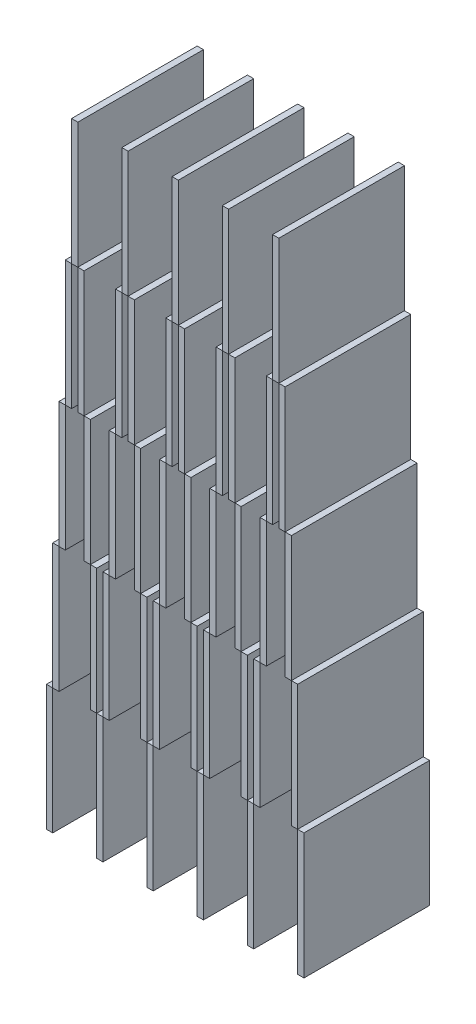
SolidWorks part; units mm, degrees
ref_plane "Front Plane" through (0, 0, 0) normal (0, 0, 1) x (1, 0, 0)
ref_plane "Top Plane" through (0, 0, 0) normal (0, 1, 0) x (1, 0, 0)
ref_plane "Right Plane" through (0, 0, 0) normal (1, 0, 0) x (0, 0, -1)
sketch "Sketch1" plane through (0, 0, 0) normal (0, 0, 1) x (1, 0, 0)
  line L361 (-45.534, 24.8846) -> (-44.534, 24.8846)
  line L362 (-46.534, 24.8846) -> (-45.534, 24.8846)
  line L363 (-46.534, 24.8846) -> (-46.534, 4.8846)
  line L364 (-46.534, 4.8846) -> (-45.534, 4.8846)
  line L365 (-45.534, 24.8846) -> (-45.534, 4.8846)
  line L366 (-45.534, 24.8846) -> (-44.534, 24.8846)
  line L367 (-45.534, 24.8846) -> (-45.534, 44.8846)
  line L368 (-45.534, 44.8846) -> (-44.534, 44.8846)
  line L369 (-44.534, 24.8846) -> (-44.534, 44.8846)
  line L371 (-44.534, 24.8846) -> (-44.534, 44.8846)
  line L372 (-44.534, 44.8846) -> (-43.534, 44.8846)
  line L374 (-38.534, 24.8846) -> (-37.534, 24.8846)
  line L379 (-38.534, 24.8846) -> (-38.534, 4.8846)
  line L384 (-38.534, 4.8846) -> (-37.534, 4.8846)
  line L389 (-37.534, 24.8846) -> (-37.534, 4.8846)
  line L392 (-40.534, 44.8846) -> (-39.534, 44.8846)
  line L393 (-39.534, 24.8846) -> (-39.534, 44.8846)
  line L394 (-37.534, 24.8846) -> (-36.534, 24.8846)
  line L395 (-39.534, 24.8846) -> (-38.534, 24.8846)
  line L396 (-39.534, 24.8846) -> (-39.534, 44.8846)
  line L397 (-39.534, 44.8846) -> (-38.534, 44.8846)
  line L398 (-38.534, 24.8846) -> (-38.534, 44.8846)
  line L399 (-45.534, 44.8846) -> (-44.534, 44.8846)
  line L400 (-45.534, 44.8846) -> (-44.534, 44.8846)
  line L403 (-44.534, 44.8846) -> (-44.534, 64.8846)
  line L404 (-44.534, 44.8846) -> (-43.534, 44.8846)
  line L405 (-44.534, 44.8846) -> (-44.534, 64.8846)
  line L406 (-44.534, 64.8846) -> (-43.534, 64.8846)
  line L407 (-43.534, 44.8846) -> (-43.534, 64.8846)
  line L408 (-44.534, 44.8846) -> (-43.534, 44.8846)
  line L410 (-43.534, 44.8846) -> (-43.534, 64.8846)
  line L411 (-43.534, 64.8846) -> (-42.534, 64.8846)
  line L413 (-37.534, 24.8846) -> (-36.534, 24.8846)
  line L418 (-37.534, 24.8846) -> (-37.534, 44.8846)
  line L421 (-41.534, 64.8846) -> (-40.534, 64.8846)
  line L422 (-40.534, 44.8846) -> (-40.534, 64.8846)
  line L423 (-37.534, 44.8846) -> (-36.534, 44.8846)
  line L424 (-40.534, 44.8846) -> (-39.534, 44.8846)
  line L425 (-40.534, 44.8846) -> (-40.534, 64.8846)
  line L426 (-40.534, 64.8846) -> (-39.534, 64.8846)
  line L427 (-39.534, 44.8846) -> (-39.534, 64.8846)
  line L428 (-40.534, 44.8846) -> (-39.534, 44.8846)
  line L429 (-39.534, 44.8846) -> (-38.534, 44.8846)
  line L430 (-39.534, 44.8846) -> (-39.534, 64.8846)
  line L433 (-36.534, 24.8846) -> (-36.534, 44.8846)
  line L438 (-44.534, 64.8846) -> (-43.534, 64.8846)
  line L441 (-43.534, 64.8846) -> (-43.534, 84.8846)
  line L442 (-44.534, 64.8846) -> (-43.534, 64.8846)
  line L443 (-43.534, 64.8846) -> (-42.534, 64.8846)
  line L444 (-43.534, 64.8846) -> (-43.534, 84.8846)
  line L445 (-43.534, 84.8846) -> (-42.534, 84.8846)
  line L446 (-42.534, 64.8846) -> (-42.534, 84.8846)
  line L447 (-43.534, 64.8846) -> (-42.534, 64.8846)
  line L449 (-42.534, 64.8846) -> (-42.534, 84.8846)
  line L450 (-42.534, 84.8846) -> (-41.534, 84.8846)
  line L451 (-41.534, 64.8846) -> (-41.534, 84.8846)
  line L452 (-36.534, 24.8846) -> (-36.534, 44.8846)
  line L453 (-41.534, 64.8846) -> (-40.534, 64.8846)
  line L454 (-41.534, 64.8846) -> (-41.534, 84.8846)
  line L455 (-41.534, 84.8846) -> (-40.534, 84.8846)
  line L456 (-40.534, 64.8846) -> (-40.534, 84.8846)
  line L457 (-41.534, 64.8846) -> (-40.534, 64.8846)
  line L458 (-40.534, 64.8846) -> (-39.534, 64.8846)
  line L459 (-40.534, 64.8846) -> (-40.534, 84.8846)
  line L462 (-40.534, 64.8846) -> (-39.534, 64.8846)
  line L467 (-36.534, 44.8846) -> (-35.534, 44.8846)
  line L476 (-32.534, 44.8846) -> (-31.534, 44.8846)
  line L477 (-43.534, 84.8846) -> (-42.534, 84.8846)
  line L480 (-42.534, 84.8846) -> (-42.534, 104.8846)
  line L481 (-43.534, 84.8846) -> (-42.534, 84.8846)
  line L482 (-42.534, 84.8846) -> (-41.534, 84.8846)
  line L483 (-42.534, 84.8846) -> (-42.534, 104.8846)
  line L484 (-42.534, 104.8846) -> (-41.534, 104.8846)
  line L485 (-41.534, 84.8846) -> (-41.534, 104.8846)
  line L486 (-42.534, 84.8846) -> (-41.534, 84.8846)
  line L487 (-41.534, 84.8846) -> (-40.534, 84.8846)
  line L488 (-41.534, 84.8846) -> (-41.534, 104.8846)
  line L491 (-41.534, 84.8846) -> (-40.534, 84.8846)
  line L496 (-31.534, 24.8846) -> (-31.534, 44.8846)
  line L501 (-44.534, 24.8846) -> (-43.534, 24.8846) [skipped]
  line L502 (-44.534, 24.8846) -> (-43.534, 24.8846) [skipped]
  line L503 (-43.534, 24.8846) -> (-43.534, 44.8846) [skipped]
  line L504 (-43.534, 24.8846) -> (-43.534, 44.8846) [skipped]
  line L505 (-42.534, 24.8846) -> (-42.534, 44.8846) [skipped]
  line L506 (-42.534, 24.8846) -> (-42.534, 44.8846) [skipped]
  line L507 (-41.534, 24.8846) -> (-41.534, 44.8846) [skipped]
  line L508 (-41.534, 24.8846) -> (-41.534, 44.8846) [skipped]
  line L509 (-40.534, 24.8846) -> (-40.534, 44.8846) [skipped]
  line L510 (-40.534, 24.8846) -> (-40.534, 44.8846) [skipped]
  line L511 (-40.534, 24.8846) -> (-39.534, 24.8846) [skipped]
  line L512 (-40.534, 24.8846) -> (-39.534, 24.8846) [skipped]
  line L513 (-41.534, 24.8846) -> (-40.534, 24.8846) [skipped]
  line L514 (-41.534, 24.8846) -> (-40.534, 24.8846) [skipped]
  line L515 (-42.534, 24.8846) -> (-41.534, 24.8846) [skipped]
  line L516 (-42.534, 24.8846) -> (-41.534, 24.8846) [skipped]
  line L517 (-43.534, 24.8846) -> (-42.534, 24.8846) [skipped]
  line L518 (-43.534, 24.8846) -> (-42.534, 24.8846) [skipped]
  line L519 (-43.534, 44.8846) -> (-42.534, 44.8846) [skipped]
  line L520 (-41.534, 44.8846) -> (-40.534, 44.8846) [skipped]
  line L521 (-42.534, 44.8846) -> (-41.534, 44.8846) [skipped]
  line L522 (-45.534, 44.8846) -> (-45.534, 64.8846) [skipped]
  line L523 (-38.534, 44.8846) -> (-38.534, 64.8846) [skipped]
  line L524 (-45.534, 64.8846) -> (-45.534, 84.8846) [skipped]
  line L525 (-44.534, 64.8846) -> (-44.534, 84.8846) [skipped]
  line L526 (-44.534, 64.8846) -> (-44.534, 84.8846) [skipped]
  line L527 (-45.534, 64.8846) -> (-44.534, 64.8846) [skipped]
  line L528 (-45.534, 64.8846) -> (-44.534, 64.8846) [skipped]
  line L529 (-45.534, 64.8846) -> (-44.534, 64.8846) [skipped]
  line L530 (-39.534, 64.8846) -> (-38.534, 64.8846) [skipped]
  line L531 (-39.534, 64.8846) -> (-38.534, 64.8846) [skipped]
  line L532 (-39.534, 64.8846) -> (-39.534, 84.8846) [skipped]
  line L533 (-39.534, 64.8846) -> (-39.534, 84.8846) [skipped]
  line L534 (-38.534, 64.8846) -> (-38.534, 84.8846) [skipped]
  line L535 (-45.534, 84.8846) -> (-45.534, 104.8846) [skipped]
  line L536 (-44.534, 84.8846) -> (-44.534, 104.8846) [skipped]
  line L537 (-44.534, 84.8846) -> (-44.534, 104.8846) [skipped]
  line L538 (-45.534, 84.8846) -> (-44.534, 84.8846) [skipped]
  line L539 (-45.534, 84.8846) -> (-44.534, 84.8846) [skipped]
  line L540 (-45.534, 84.8846) -> (-44.534, 84.8846) [skipped]
  line L541 (-44.534, 84.8846) -> (-43.534, 84.8846) [skipped]
  line L542 (-40.534, 84.8846) -> (-39.534, 84.8846) [skipped]
  line L543 (-39.534, 84.8846) -> (-39.534, 104.8846) [skipped]
  line L544 (-39.534, 84.8846) -> (-39.534, 104.8846) [skipped]
  line L545 (-39.534, 84.8846) -> (-38.534, 84.8846) [skipped]
  line L546 (-39.534, 84.8846) -> (-38.534, 84.8846) [skipped]
  line L547 (-38.534, 84.8846) -> (-38.534, 104.8846) [skipped]
  line L548 (-45.534, 104.8846) -> (-44.534, 104.8846) [skipped]
  line L549 (-44.534, 104.8846) -> (-43.534, 104.8846) [skipped]
  line L550 (-40.534, 104.8846) -> (-39.534, 104.8846) [skipped]
  line L551 (-39.534, 104.8846) -> (-38.534, 104.8846) [skipped]
  line L552 (-31.534, 24.8846) -> (-30.534, 24.8846)
  line L553 (-31.534, 24.8846) -> (-31.534, 44.8846)
  line L554 (-31.534, 44.8846) -> (-30.534, 44.8846)
  line L555 (-30.534, 24.8846) -> (-30.534, 44.8846)
  line L556 (-37.534, 44.8846) -> (-36.534, 44.8846)
  line L557 (-37.534, 44.8846) -> (-36.534, 44.8846)
  line L558 (-36.534, 44.8846) -> (-35.534, 44.8846)
  line L559 (-36.534, 44.8846) -> (-35.534, 44.8846)
  line L560 (-32.534, 44.8846) -> (-31.534, 44.8846)
  line L561 (-32.534, 44.8846) -> (-31.534, 44.8846)
  line L562 (-31.534, 44.8846) -> (-30.534, 44.8846)
  line L563 (-36.534, 44.8846) -> (-36.534, 64.8846)
  line L564 (-36.534, 44.8846) -> (-36.534, 64.8846)
  line L565 (-36.534, 64.8846) -> (-35.534, 64.8846)
  line L566 (-35.534, 44.8846) -> (-35.534, 64.8846)
  line L567 (-35.534, 44.8846) -> (-35.534, 64.8846)
  line L568 (-35.534, 64.8846) -> (-34.534, 64.8846)
  line L569 (-33.534, 64.8846) -> (-32.534, 64.8846)
  line L570 (-32.534, 44.8846) -> (-32.534, 64.8846)
  line L571 (-32.534, 44.8846) -> (-32.534, 64.8846)
  line L572 (-32.534, 64.8846) -> (-31.534, 64.8846)
  line L573 (-31.534, 44.8846) -> (-31.534, 64.8846)
  line L574 (-31.534, 44.8846) -> (-31.534, 64.8846)
  line L575 (-36.534, 64.8846) -> (-35.534, 64.8846)
  line L576 (-35.534, 64.8846) -> (-35.534, 84.8846)
  line L577 (-36.534, 64.8846) -> (-35.534, 64.8846)
  line L578 (-35.534, 64.8846) -> (-34.534, 64.8846)
  line L579 (-35.534, 64.8846) -> (-35.534, 84.8846)
  line L580 (-35.534, 84.8846) -> (-34.534, 84.8846)
  line L581 (-34.534, 64.8846) -> (-34.534, 84.8846)
  line L582 (-35.534, 64.8846) -> (-34.534, 64.8846)
  line L583 (-34.534, 64.8846) -> (-34.534, 84.8846)
  line L584 (-34.534, 84.8846) -> (-33.534, 84.8846)
  line L585 (-33.534, 64.8846) -> (-33.534, 84.8846)
  line L586 (-33.534, 64.8846) -> (-32.534, 64.8846)
  line L587 (-33.534, 64.8846) -> (-33.534, 84.8846)
  line L588 (-33.534, 84.8846) -> (-32.534, 84.8846)
  line L589 (-32.534, 64.8846) -> (-32.534, 84.8846)
  line L590 (-33.534, 64.8846) -> (-32.534, 64.8846)
  line L591 (-32.534, 64.8846) -> (-31.534, 64.8846)
  line L592 (-32.534, 64.8846) -> (-32.534, 84.8846)
  line L593 (-32.534, 64.8846) -> (-31.534, 64.8846)
  line L594 (-35.534, 84.8846) -> (-34.534, 84.8846)
  line L595 (-34.534, 84.8846) -> (-34.534, 104.8846)
  line L596 (-35.534, 84.8846) -> (-34.534, 84.8846)
  line L597 (-34.534, 84.8846) -> (-33.534, 84.8846)
  line L598 (-34.534, 84.8846) -> (-34.534, 104.8846)
  line L599 (-34.534, 104.8846) -> (-33.534, 104.8846)
  line L600 (-33.534, 84.8846) -> (-33.534, 104.8846)
  line L601 (-34.534, 84.8846) -> (-33.534, 84.8846)
  line L602 (-33.534, 84.8846) -> (-32.534, 84.8846)
  line L603 (-33.534, 84.8846) -> (-33.534, 104.8846)
  line L604 (-33.534, 84.8846) -> (-32.534, 84.8846)
  line L605 (-29.534, 24.8846) -> (-28.534, 24.8846)
  line L606 (-29.534, 24.8846) -> (-28.534, 24.8846)
  line L607 (-29.534, 24.8846) -> (-29.534, 44.8846)
  line L608 (-29.534, 44.8846) -> (-28.534, 44.8846)
  line L609 (-28.534, 24.8846) -> (-28.534, 44.8846)
  line L610 (-28.534, 24.8846) -> (-28.534, 44.8846)
  line L611 (-28.534, 44.8846) -> (-27.534, 44.8846)
  line L612 (-24.534, 44.8846) -> (-23.534, 44.8846)
  line L613 (-23.534, 24.8846) -> (-23.534, 44.8846)
  line L614 (-23.534, 24.8846) -> (-22.534, 24.8846)
  line L615 (-23.534, 24.8846) -> (-23.534, 44.8846)
  line L616 (-23.534, 44.8846) -> (-22.534, 44.8846)
  line L617 (-22.534, 24.8846) -> (-22.534, 44.8846)
  line L618 (-29.534, 44.8846) -> (-28.534, 44.8846)
  line L619 (-29.534, 44.8846) -> (-28.534, 44.8846)
  line L620 (-28.534, 44.8846) -> (-27.534, 44.8846)
  line L621 (-28.534, 44.8846) -> (-27.534, 44.8846)
  line L622 (-24.534, 44.8846) -> (-23.534, 44.8846)
  line L623 (-24.534, 44.8846) -> (-23.534, 44.8846)
  line L624 (-23.534, 44.8846) -> (-22.534, 44.8846)
  line L625 (-28.534, 44.8846) -> (-28.534, 64.8846)
  line L626 (-28.534, 44.8846) -> (-28.534, 64.8846)
  line L627 (-28.534, 64.8846) -> (-27.534, 64.8846)
  line L628 (-27.534, 44.8846) -> (-27.534, 64.8846)
  line L629 (-27.534, 44.8846) -> (-27.534, 64.8846)
  line L630 (-27.534, 64.8846) -> (-26.534, 64.8846)
  line L631 (-25.534, 64.8846) -> (-24.534, 64.8846)
  line L632 (-24.534, 44.8846) -> (-24.534, 64.8846)
  line L633 (-24.534, 44.8846) -> (-24.534, 64.8846)
  line L634 (-24.534, 64.8846) -> (-23.534, 64.8846)
  line L635 (-23.534, 44.8846) -> (-23.534, 64.8846)
  line L636 (-23.534, 44.8846) -> (-23.534, 64.8846)
  line L637 (-28.534, 64.8846) -> (-27.534, 64.8846)
  line L638 (-27.534, 64.8846) -> (-27.534, 84.8846)
  line L639 (-28.534, 64.8846) -> (-27.534, 64.8846)
  line L640 (-27.534, 64.8846) -> (-26.534, 64.8846)
  line L641 (-27.534, 64.8846) -> (-27.534, 84.8846)
  line L642 (-27.534, 84.8846) -> (-26.534, 84.8846)
  line L643 (-26.534, 64.8846) -> (-26.534, 84.8846)
  line L644 (-27.534, 64.8846) -> (-26.534, 64.8846)
  line L645 (-26.534, 64.8846) -> (-26.534, 84.8846)
  line L646 (-26.534, 84.8846) -> (-25.534, 84.8846)
  line L647 (-25.534, 64.8846) -> (-25.534, 84.8846)
  line L648 (-25.534, 64.8846) -> (-24.534, 64.8846)
  line L649 (-25.534, 64.8846) -> (-25.534, 84.8846)
  line L650 (-25.534, 84.8846) -> (-24.534, 84.8846)
  line L651 (-24.534, 64.8846) -> (-24.534, 84.8846)
  line L652 (-25.534, 64.8846) -> (-24.534, 64.8846)
  line L653 (-24.534, 64.8846) -> (-23.534, 64.8846)
  line L654 (-24.534, 64.8846) -> (-24.534, 84.8846)
  line L655 (-24.534, 64.8846) -> (-23.534, 64.8846)
  line L656 (-27.534, 84.8846) -> (-26.534, 84.8846)
  line L657 (-26.534, 84.8846) -> (-26.534, 104.8846)
  line L658 (-27.534, 84.8846) -> (-26.534, 84.8846)
  line L659 (-26.534, 84.8846) -> (-25.534, 84.8846)
  line L660 (-26.534, 84.8846) -> (-26.534, 104.8846)
  line L661 (-26.534, 104.8846) -> (-25.534, 104.8846)
  line L662 (-25.534, 84.8846) -> (-25.534, 104.8846)
  line L663 (-26.534, 84.8846) -> (-25.534, 84.8846)
  line L664 (-25.534, 84.8846) -> (-24.534, 84.8846)
  line L665 (-25.534, 84.8846) -> (-25.534, 104.8846)
  line L666 (-25.534, 84.8846) -> (-24.534, 84.8846)
  line L667 (-21.534, 24.8846) -> (-20.534, 24.8846)
  line L668 (-21.534, 24.8846) -> (-20.534, 24.8846)
  line L669 (-21.534, 24.8846) -> (-21.534, 44.8846)
  line L670 (-21.534, 44.8846) -> (-20.534, 44.8846)
  line L671 (-20.534, 24.8846) -> (-20.534, 44.8846)
  line L672 (-20.534, 24.8846) -> (-20.534, 44.8846)
  line L673 (-20.534, 44.8846) -> (-19.534, 44.8846)
  line L674 (-16.534, 44.8846) -> (-15.534, 44.8846)
  line L675 (-15.534, 24.8846) -> (-15.534, 44.8846)
  line L676 (-15.534, 24.8846) -> (-14.534, 24.8846)
  line L677 (-15.534, 24.8846) -> (-15.534, 44.8846)
  line L678 (-15.534, 44.8846) -> (-14.534, 44.8846)
  line L679 (-14.534, 24.8846) -> (-14.534, 44.8846)
  line L680 (-21.534, 44.8846) -> (-20.534, 44.8846)
  line L681 (-21.534, 44.8846) -> (-20.534, 44.8846)
  line L682 (-20.534, 44.8846) -> (-19.534, 44.8846)
  line L683 (-20.534, 44.8846) -> (-19.534, 44.8846)
  line L684 (-16.534, 44.8846) -> (-15.534, 44.8846)
  line L685 (-16.534, 44.8846) -> (-15.534, 44.8846)
  line L686 (-15.534, 44.8846) -> (-14.534, 44.8846)
  line L687 (-20.534, 44.8846) -> (-20.534, 64.8846)
  line L688 (-20.534, 44.8846) -> (-20.534, 64.8846)
  line L689 (-20.534, 64.8846) -> (-19.534, 64.8846)
  line L690 (-19.534, 44.8846) -> (-19.534, 64.8846)
  line L691 (-19.534, 44.8846) -> (-19.534, 64.8846)
  line L692 (-19.534, 64.8846) -> (-18.534, 64.8846)
  line L693 (-17.534, 64.8846) -> (-16.534, 64.8846)
  line L694 (-16.534, 44.8846) -> (-16.534, 64.8846)
  line L695 (-16.534, 44.8846) -> (-16.534, 64.8846)
  line L696 (-16.534, 64.8846) -> (-15.534, 64.8846)
  line L697 (-15.534, 44.8846) -> (-15.534, 64.8846)
  line L698 (-15.534, 44.8846) -> (-15.534, 64.8846)
  line L699 (-20.534, 64.8846) -> (-19.534, 64.8846)
  line L700 (-19.534, 64.8846) -> (-19.534, 84.8846)
  line L701 (-20.534, 64.8846) -> (-19.534, 64.8846)
  line L702 (-19.534, 64.8846) -> (-18.534, 64.8846)
  line L703 (-19.534, 64.8846) -> (-19.534, 84.8846)
  line L704 (-19.534, 84.8846) -> (-18.534, 84.8846)
  line L705 (-18.534, 64.8846) -> (-18.534, 84.8846)
  line L706 (-19.534, 64.8846) -> (-18.534, 64.8846)
  line L707 (-18.534, 64.8846) -> (-18.534, 84.8846)
  line L708 (-18.534, 84.8846) -> (-17.534, 84.8846)
  line L709 (-17.534, 64.8846) -> (-17.534, 84.8846)
  line L710 (-17.534, 64.8846) -> (-16.534, 64.8846)
  line L711 (-17.534, 64.8846) -> (-17.534, 84.8846)
  line L712 (-17.534, 84.8846) -> (-16.534, 84.8846)
  line L713 (-16.534, 64.8846) -> (-16.534, 84.8846)
  line L714 (-17.534, 64.8846) -> (-16.534, 64.8846)
  line L715 (-16.534, 64.8846) -> (-15.534, 64.8846)
  line L716 (-16.534, 64.8846) -> (-16.534, 84.8846)
  line L717 (-16.534, 64.8846) -> (-15.534, 64.8846)
  line L718 (-19.534, 84.8846) -> (-18.534, 84.8846)
  line L719 (-18.534, 84.8846) -> (-18.534, 104.8846)
  line L720 (-19.534, 84.8846) -> (-18.534, 84.8846)
  line L721 (-18.534, 84.8846) -> (-17.534, 84.8846)
  line L722 (-18.534, 84.8846) -> (-18.534, 104.8846)
  line L723 (-18.534, 104.8846) -> (-17.534, 104.8846)
  line L724 (-17.534, 84.8846) -> (-17.534, 104.8846)
  line L725 (-18.534, 84.8846) -> (-17.534, 84.8846)
  line L726 (-17.534, 84.8846) -> (-16.534, 84.8846)
  line L727 (-17.534, 84.8846) -> (-17.534, 104.8846)
  line L728 (-17.534, 84.8846) -> (-16.534, 84.8846)
  line L729 (-13.534, 24.8846) -> (-12.534, 24.8846)
  line L730 (-13.534, 24.8846) -> (-12.534, 24.8846)
  line L731 (-13.534, 24.8846) -> (-13.534, 44.8846)
  line L732 (-13.534, 44.8846) -> (-12.534, 44.8846)
  line L733 (-12.534, 24.8846) -> (-12.534, 44.8846)
  line L734 (-12.534, 24.8846) -> (-12.534, 44.8846)
  line L735 (-12.534, 44.8846) -> (-11.534, 44.8846)
  line L736 (-8.534, 44.8846) -> (-7.534, 44.8846)
  line L737 (-7.534, 24.8846) -> (-7.534, 44.8846)
  line L738 (-7.534, 24.8846) -> (-6.534, 24.8846)
  line L739 (-7.534, 24.8846) -> (-7.534, 44.8846)
  line L740 (-7.534, 44.8846) -> (-6.534, 44.8846)
  line L741 (-6.534, 24.8846) -> (-6.534, 44.8846)
  line L742 (-13.534, 44.8846) -> (-12.534, 44.8846)
  line L743 (-13.534, 44.8846) -> (-12.534, 44.8846)
  line L744 (-12.534, 44.8846) -> (-11.534, 44.8846)
  line L745 (-12.534, 44.8846) -> (-11.534, 44.8846)
  line L746 (-8.534, 44.8846) -> (-7.534, 44.8846)
  line L747 (-8.534, 44.8846) -> (-7.534, 44.8846)
  line L748 (-7.534, 44.8846) -> (-6.534, 44.8846)
  line L749 (-12.534, 44.8846) -> (-12.534, 64.8846)
  line L750 (-12.534, 44.8846) -> (-12.534, 64.8846)
  line L751 (-12.534, 64.8846) -> (-11.534, 64.8846)
  line L752 (-11.534, 44.8846) -> (-11.534, 64.8846)
  line L753 (-11.534, 44.8846) -> (-11.534, 64.8846)
  line L754 (-11.534, 64.8846) -> (-10.534, 64.8846)
  line L755 (-9.534, 64.8846) -> (-8.534, 64.8846)
  line L756 (-8.534, 44.8846) -> (-8.534, 64.8846)
  line L757 (-8.534, 44.8846) -> (-8.534, 64.8846)
  line L758 (-8.534, 64.8846) -> (-7.534, 64.8846)
  line L759 (-7.534, 44.8846) -> (-7.534, 64.8846)
  line L760 (-7.534, 44.8846) -> (-7.534, 64.8846)
  line L761 (-12.534, 64.8846) -> (-11.534, 64.8846)
  line L762 (-11.534, 64.8846) -> (-11.534, 84.8846)
  line L763 (-12.534, 64.8846) -> (-11.534, 64.8846)
  line L764 (-11.534, 64.8846) -> (-10.534, 64.8846)
  line L765 (-11.534, 64.8846) -> (-11.534, 84.8846)
  line L766 (-11.534, 84.8846) -> (-10.534, 84.8846)
  line L767 (-10.534, 64.8846) -> (-10.534, 84.8846)
  line L768 (-11.534, 64.8846) -> (-10.534, 64.8846)
  line L769 (-10.534, 64.8846) -> (-10.534, 84.8846)
  line L770 (-10.534, 84.8846) -> (-9.534, 84.8846)
  line L771 (-9.534, 64.8846) -> (-9.534, 84.8846)
  line L772 (-9.534, 64.8846) -> (-8.534, 64.8846)
  line L773 (-9.534, 64.8846) -> (-9.534, 84.8846)
  line L774 (-9.534, 84.8846) -> (-8.534, 84.8846)
  line L775 (-8.534, 64.8846) -> (-8.534, 84.8846)
  line L776 (-9.534, 64.8846) -> (-8.534, 64.8846)
  line L777 (-8.534, 64.8846) -> (-7.534, 64.8846)
  line L778 (-8.534, 64.8846) -> (-8.534, 84.8846)
  line L779 (-8.534, 64.8846) -> (-7.534, 64.8846)
  line L780 (-11.534, 84.8846) -> (-10.534, 84.8846)
  line L781 (-10.534, 84.8846) -> (-10.534, 104.8846)
  line L782 (-11.534, 84.8846) -> (-10.534, 84.8846)
  line L783 (-10.534, 84.8846) -> (-9.534, 84.8846)
  line L784 (-10.534, 84.8846) -> (-10.534, 104.8846)
  line L785 (-10.534, 104.8846) -> (-9.534, 104.8846)
  line L786 (-9.534, 84.8846) -> (-9.534, 104.8846)
  line L787 (-10.534, 84.8846) -> (-9.534, 84.8846)
  line L788 (-9.534, 84.8846) -> (-8.534, 84.8846)
  line L789 (-9.534, 84.8846) -> (-9.534, 104.8846)
  line L790 (-9.534, 84.8846) -> (-8.534, 84.8846)
  line L791 (-30.534, 24.8846) -> (-29.534, 24.8846)
  line L792 (-30.534, 24.8846) -> (-30.534, 4.8846)
  line L793 (-30.534, 4.8846) -> (-29.534, 4.8846)
  line L794 (-29.534, 24.8846) -> (-29.534, 4.8846)
  line L795 (-22.534, 24.8846) -> (-21.534, 24.8846)
  line L796 (-22.534, 24.8846) -> (-22.534, 4.8846)
  line L797 (-22.534, 4.8846) -> (-21.534, 4.8846)
  line L798 (-21.534, 24.8846) -> (-21.534, 4.8846)
  line L799 (-14.534, 24.8846) -> (-13.534, 24.8846)
  line L800 (-14.534, 24.8846) -> (-14.534, 4.8846)
  line L801 (-14.534, 4.8846) -> (-13.534, 4.8846)
  line L802 (-13.534, 24.8846) -> (-13.534, 4.8846)
  line L803 (-6.534, 24.8846) -> (-5.534, 24.8846)
  line L804 (-6.534, 24.8846) -> (-6.534, 4.8846)
  line L805 (-6.534, 4.8846) -> (-5.534, 4.8846)
  line L806 (-5.534, 24.8846) -> (-5.534, 4.8846)
  dimension "D1" = 7
  dimension "D2" = 4
  dimension "D5" = 2
extrude "Boss-Extrude1" add sketch "Sketch1" along normal blind 20 contours L365 L362 L363 L364 | L361 L369 L368 L367 | L395 L398 L397 L393 | L394 L433 L423 L418 | L389 L374 L379 L384 | L552 L555 L554 L496 | L605 L609 L608 L607 | L794 L791 L792 L793 | L614 L617 L616 L613 | L667 L671 L670 L669 | L798 L795 L796 L797 | L806 L803 L804 L805 | L802 L799 L800 L801 | L676 L679 L678 L675 | L729 L733 L732 L731 | L738 L741 L740 L737 | L372 L407 L406 L403 | L467 L566 L565 L563 | L476 L573 L572 L570 | L411 L446 L445 L441 | L421 L456 L455 L451 | L568 L581 L580 L576 | L569 L589 L588 L585 | L611 L628 L627 L625 | L630 L643 L642 L638 | L631 L651 L650 L647 | L612 L635 L634 L632 | L673 L690 L689 L687 | L692 L705 L704 L700 | L693 L713 L712 L709 | L674 L697 L696 L694 | L735 L752 L751 L749 | L754 L767 L766 L762 | L755 L775 L774 L771 | L736 L759 L758 L756 | L450 L485 L484 L480 | L584 L600 L599 L595 | L646 L662 L661 L657 | L708 L724 L723 L719 | L770 L786 L785 L781 | L427 L426 L425 L424
